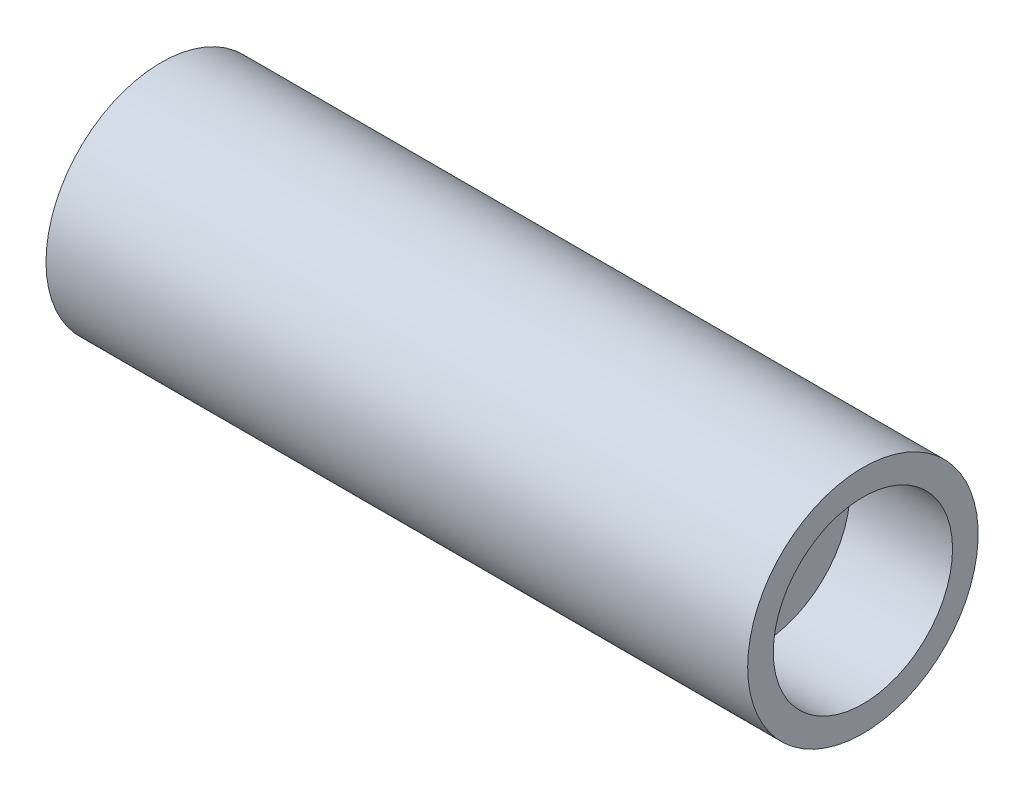
SolidWorks part; units mm, degrees
material "Brass"
ref_plane "Front Plane" through (0, 0, 0) normal (0, 0, 1) x (1, 0, 0)
ref_plane "Top Plane" through (0, 0, 0) normal (0, 1, 0) x (1, 0, 0)
ref_plane "Right Plane" through (0, 0, 0) normal (1, 0, 0) x (0, 0, -1)
sketch "Sketch1" plane through (0, 0, 0) normal (0, 0, 1) x (1, 0, 0)
  line L0 (-6.4955, 0) -> (6.4955, 0) construction
  line L1 (0, 3.9606) -> (0, -3.9606) construction
  line L2 (9.7, 3.5) -> (13.7, 3.5)
  line L3 (-13.7, 4.5) -> (13.7, 4.5)
  line L4 (-13.7, 4.5) -> (-13.7, 3.5)
  line L5 (-13.7, 3.5) -> (-9.7, 3.5)
  line L6 (13.7, 4.5) -> (13.7, 3.5)
  line L7 (-13.7, 4.5) -> (13.7, 3.5) construction
  line L8 (-13.7, 3.5) -> (13.7, 4.5) construction
  line L10 (-9.7, 3.5) -> (-9.7, 2)
  line L11 (-9.7, 2) -> (9.7, 2)
  line L12 (9.7, 3.5) -> (9.7, 2)
  point P0 (0, 4)
  point P4 (0, 0)
  point P8 (0, 0)
  point P17 (13.7, 4)
  dimension "D1" = 7
  dimension "D2" = 9
  dimension "D3" = 27.4
  dimension "D4" = 4
  dimension "D5" = 4
  dimension "D6" = 4
revolve "Revolve1" add sketch "Sketch1" angle 360 about L0
